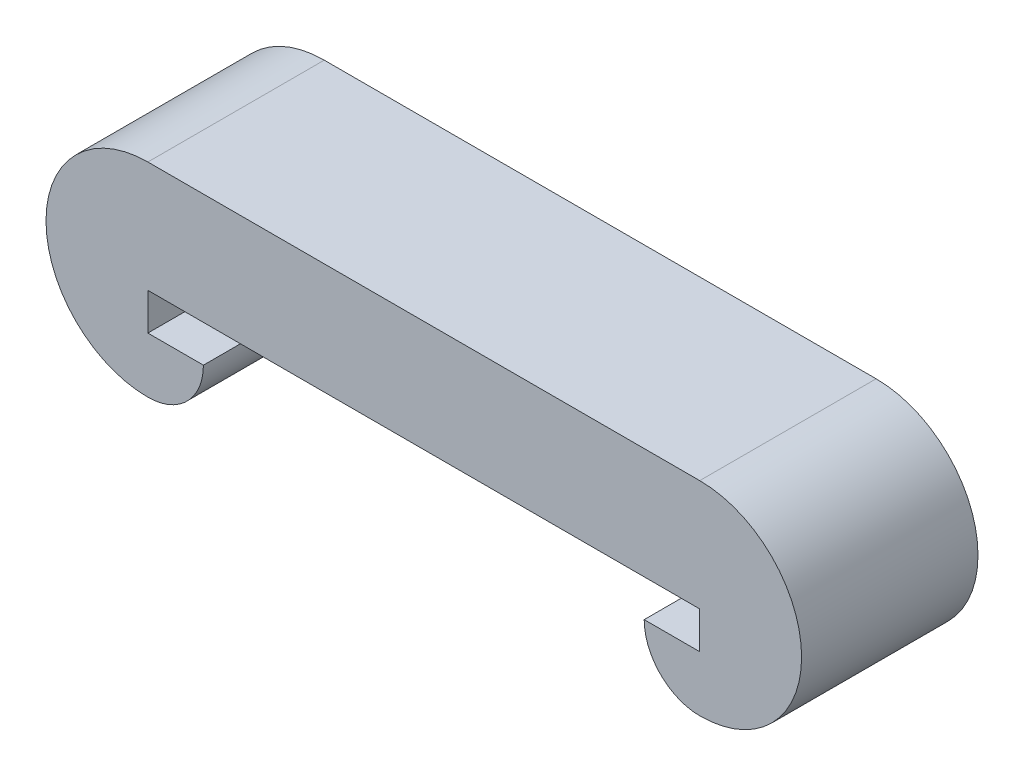
SolidWorks part; units mm, degrees
ref_plane "Front Plane" through (0, 0, 0) normal (0, 0, 1) x (1, 0, 0)
ref_plane "Top Plane" through (0, 0, 0) normal (0, 1, 0) x (1, 0, 0)
ref_plane "Right Plane" through (0, 0, 0) normal (1, 0, 0) x (0, 0, -1)
sketch "Sketch1" plane through (0, 0, 0) normal (0, 0, 1) x (1, 0, 0)
  line L0 (-7.45, 3) -> (0, 3)
  line L1 (-7.45, 0) -> (0, 0)
  line L2 (-7.45, 0) -> (-7.45, -1)
  line L3 (-7.45, -1) -> (-5.95, -1)
  line L5 (0, 0) -> (0, 3)
  arc A0 (-5.95, -1) -> (-7.45, -2.5) centre (-7.45, -1) cw
  arc A1 (-7.45, -2.5) -> (-7.45, 3) centre (-7.45, 0.25) cw
  dimension "D1" = 7.45
  dimension "D2" = 1
  dimension "D3" = 3
  dimension "D4" = 1.5
extrude "Boss-Extrude1" add sketch "Sketch1" along normal blind 4.7625
mirror "Mirror1" about plane through (0, 0, 4.7625) normal (-1, 0, 0) of "Boss-Extrude1"
